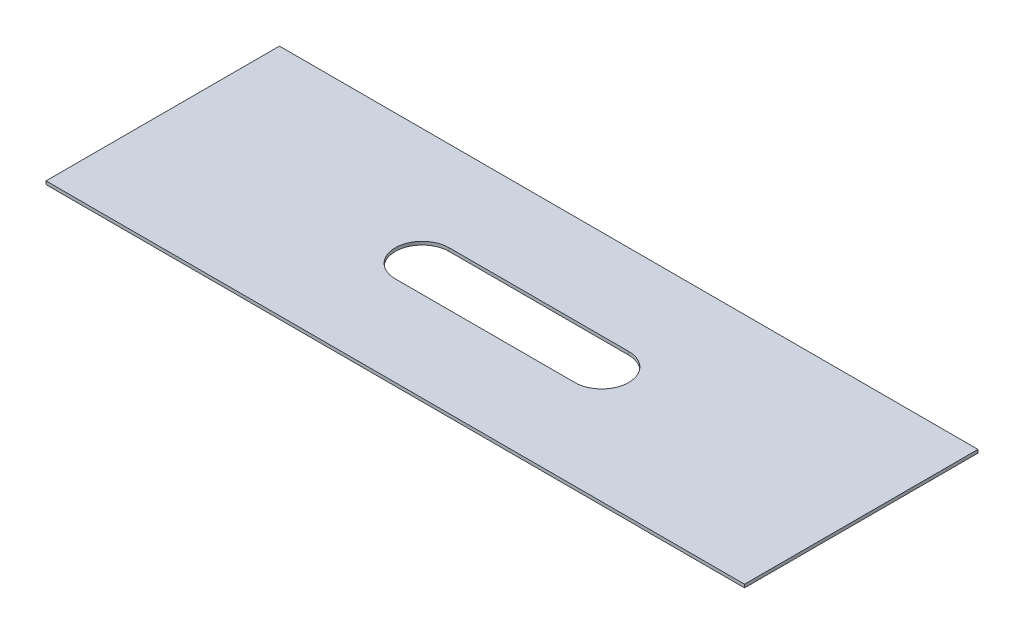
SolidWorks part; units mm, degrees
ref_plane "Front Plane" through (0, 0, 0) normal (0, 0, 1) x (1, 0, 0)
ref_plane "Top Plane" through (0, 0, 0) normal (0, 1, 0) x (1, 0, 0)
ref_plane "Right Plane" through (0, 0, 0) normal (1, 0, 0) x (0, 0, -1)
sketch "Sketch1" plane through (0, 0, 0) normal (0, 1, 0) x (1, 0, 0)
  line L1 (-49.403, 16.51) -> (49.403, 16.51)
  line L2 (-49.403, 16.51) -> (-49.403, -16.51)
  line L3 (-49.403, -16.51) -> (49.403, -16.51)
  line L4 (49.403, 16.51) -> (49.403, -16.51)
  point P4 (0, 16.51)
  point P5 (-49.403, 0)
  dimension "D1" = 98.806
  dimension "D2" = 33.02
extrude "Boss-Extrude1" add sketch "Sketch1" along normal blind 0.4572
sketch "Sketch2" plane through (0, 0.4572, 0) normal (0, 1, 0) x (1, 0, 0)
  line L0 (-12.7, 0) -> (12.7, 0) construction
  line L1 (-12.7, 3.81) -> (12.7, 3.81)
  line L2 (-12.7, -3.81) -> (12.7, -3.81)
  arc A0 (-12.7, 3.81) -> (-12.7, -3.81) centre (-12.7, 0) ccw
  arc A1 (12.7, -3.81) -> (12.7, 3.81) centre (12.7, 0) ccw
  point P3 (0, 0)
  point P8 (0, 0)
  dimension "D2" = 3.81
  dimension "D1" = 25.4
extrude "Cut-Extrude1" cut sketch "Sketch2" against normal through all
